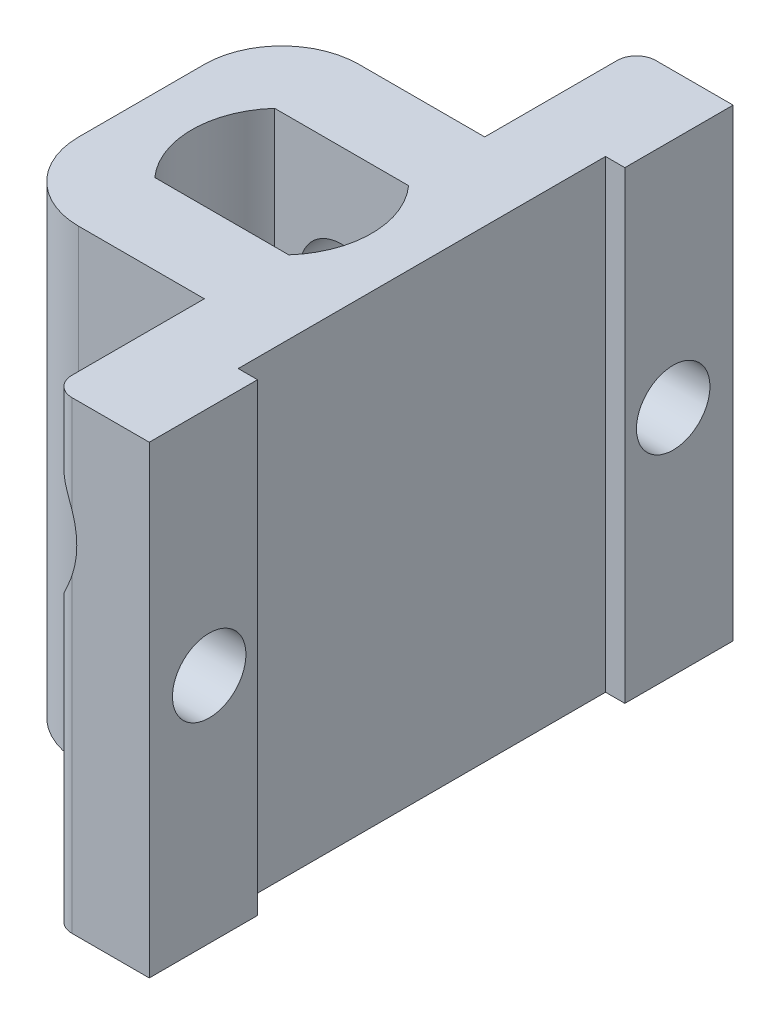
SolidWorks part; units mm, degrees
ref_plane "前视基准面" through (0, 0, 0) normal (0, 0, 1) x (1, 0, 0)
ref_plane "上视基准面" through (0, 0, 0) normal (0, 1, 0) x (1, 0, 0)
ref_plane "右视基准面" through (0, 0, 0) normal (1, 0, 0) x (0, 0, -1)
sketch "草图1" plane through (0, 0, 0) normal (0, 1, 0) x (1, 0, 0)
  line L0 (-7.3527, 0) -> (8.6949, 0) construction
  line L1 (-3.4659, -3.1) -> (3.4659, -3.1)
  line L2 (-3.4659, 3.1) -> (3.4659, 3.1)
  line L3 (-7.3527, -3.1) -> (8.6949, -3.1) construction
  line L4 (-7.3527, 3.1) -> (8.6949, 3.1) construction
  line L5 (-4.5, -6) -> (4.5, -6)
  line L6 (-4.5, 6) -> (4.5, 6)
  line L7 (-7.3527, 6) -> (8.6949, 6) construction
  line L8 (-7.3527, -6) -> (8.6949, -6) construction
  line L10 (-7.25, -7.25) -> (7.25, -7.25)
  line L11 (-7.25, -7.25) -> (-7.25, 7.25)
  line L12 (-7.25, 7.25) -> (7.25, 7.25)
  line L13 (7.25, -7.25) -> (7.25, 7.25)
  line L14 (0, 7.25) -> (0, -7.25) construction
  line L15 (-7.25, 0) -> (7.25, 0) construction
  arc A0 (-3.4659, 3.1) -> (-3.4659, -3.1) centre (0, 0) ccw
  arc A1 (3.4659, -3.1) -> (3.4659, 3.1) centre (0, 0) ccw
  arc A2 (4.5, -6) -> (4.5, 6) centre (0, 0) ccw construction
  arc A3 (-4.5, 6) -> (-4.5, -6) centre (0, 0) ccw construction
  dimension "D1" = 9.3
  dimension "D4" = 15
  dimension "D5" = 14.5
  dimension "D6" = 14.5
  dimension "D2" = 3.1
  dimension "D3" = 3.1
extrude "凸台-拉伸1" add sketch "草图1" along normal blind 10.5 contours L10 L13 L12 L6 L11 L5 A1 L1 A0 L2
sketch "草图4" plane through (0, 0, 0) normal (0, 0, 1) x (1, 0, 0)
  line L0 (0, 12.915) -> (0, -4.1472) construction
  line L1 (-7.25, 0) -> (7.25, 0) construction
  circle A0 centre (0, 4) radius 2.15
  dimension "D1" = 4.3
  dimension "D2" = 4
extrude "切除-拉伸2" cut sketch "草图4" against normal through all both and the other way through all
sketch "草图6" plane through (0, 0, 0) normal (0, -1, 0) x (1, 0, 0)
  line L0 (-3.4659, -3.1) -> (3.4659, -3.1) construction
  line L1 (-3.4659, 3.1) -> (3.4659, 3.1) construction
  line L2 (-3.4659, -3.1) -> (3.4659, -3.1)
  line L3 (-3.4659, 3.1) -> (3.4659, 3.1)
  line L4 (7.25, 7.25) -> (-7.25, 7.25)
  line L5 (-7.25, 7.25) -> (-7.25, -7.25)
  line L6 (-7.25, -7.25) -> (7.25, -7.25)
  line L7 (7.25, -7.25) -> (7.25, 7.25)
  line L8 (7.25, 7.25) -> (-7.25, 7.25)
  line L9 (-7.25, 7.25) -> (-7.25, -7.25)
  line L10 (-7.25, -7.25) -> (7.25, -7.25)
  line L11 (7.25, -7.25) -> (7.25, 7.25)
  arc A0 (3.4659, -3.1) -> (3.4659, 3.1) centre (0, 0) ccw construction
  arc A1 (-3.4659, 3.1) -> (-3.4659, -3.1) centre (0, 0) ccw construction
  arc A2 (3.4659, -3.1) -> (3.4659, 3.1) centre (0, 0) ccw
  arc A3 (-3.4659, 3.1) -> (-3.4659, -3.1) centre (0, 0) ccw
  dimension "D1" = 0
extrude "凸台-拉伸2" add sketch "草图6" along normal blind 13.5
sketch "草图9" plane through (0, 0, -3.1) normal (0, 0, 1) x (1, 0, 0)
  line L0 (7.25, 10.5) -> (7.25, -13.5)
  line L1 (7.25, 10.5) -> (7.25, -13.5)
  line L2 (-7.25, -13.5) -> (7.25, -13.5) construction
  line L3 (7.25, 10.5) -> (3.25, 10.5)
  line L4 (7.25, 10.5) -> (7.25, -13.5)
  line L5 (7.25, -13.5) -> (3.25, -13.5)
  line L6 (3.25, 10.5) -> (3.25, -13.5)
  line M6 (3.4659, -13.5) -> (3.4659, 10.5)
  dimension "D2" = 4
extrude "凸台-拉伸3" add sketch "草图9" against normal blind 12 contours L5 L1 L3 M6
mirror "镜向1" about plane through (0, 0, 0) normal (0, 0, 1) of "凸台-拉伸3"
sketch "草图10" plane through (7.25, 0, 0) normal (1, 0, 0) x (0, 0, -1)
  line L5 (15.1, -13.5) -> (-15.1, -13.5) construction
  line L6 (-15.1, 10.5) -> (-9.5, 10.5)
  line L7 (-15.1, 10.5) -> (-15.1, -13.5)
  line L8 (-15.1, -13.5) -> (-9.5, -13.5)
  line L9 (-9.5, 10.5) -> (-9.5, -13.5)
  line L10 (0, 22.1549) -> (0, -15.2155) construction
  line L11 (15.1, 10.5) -> (9.5, 10.5)
  line L12 (15.1, 10.5) -> (15.1, -13.5)
  line L13 (15.1, -13.5) -> (9.5, -13.5)
  line L14 (9.5, 10.5) -> (9.5, -13.5)
  dimension "D1" = 9.5
  dimension "D2" = 19
extrude "凸台-拉伸4" add sketch "草图10" along normal blind 1
sketch "草图11" plane through (0, 0, 15.1) normal (0, 0, 1) x (1, 0, 0)
  circle A0 centre (0, 4) radius 2.15 construction
  circle A1 centre (0, 4) radius 2.15 construction
  circle A2 centre (0, 4) radius 4.5
  dimension "D1" = 9
extrude "切除-拉伸3" cut sketch "草图11" against normal blind 7.85
mirror "镜向2" about plane through (0, 0, 0) normal (0, 0, 1) of "切除-拉伸3"
sketch "草图12" plane through (8.25, 0, 0) normal (1, 0, 0) x (0, 0, -1)
  line L0 (15.1, -1.5) -> (-15.1, -1.5) construction
  line L1 (15.1, -13.5) -> (15.1, 10.5) construction
  line L2 (-15.1, 10.5) -> (-15.1, -13.5) construction
  line L3 (0, 16.5479) -> (0, -12.8351) construction
  line L4 (-12.3, 10.5) -> (-12.3, -13.5) construction
  line L6 (-9.5, 10.5) -> (-15.1, 10.5) construction
  line L7 (-15.1, -13.5) -> (-9.5, -13.5) construction
  circle A1 centre (12, -1.5) radius 1.9
  circle A2 centre (-12, -1.5) radius 1.9
  dimension "D1" = 3.8
  dimension "D2" = 3.8
  dimension "D4" = 12
  dimension "D3" = 12
extrude "切除-拉伸4" cut sketch "草图12" against normal through all both and the other way through all
fillet "圆角1" radius 4 2 edges at (-7.25, -1.5, -7.25) (-7.25, -1.5, 7.25)
fillet "圆角3" radius 1 4 edges at (3.25, 8.8062, 15.1) (3.25, -6.3062, 15.1) (3.25, 8.8062, -15.1) (3.25, -6.3062, -15.1)
